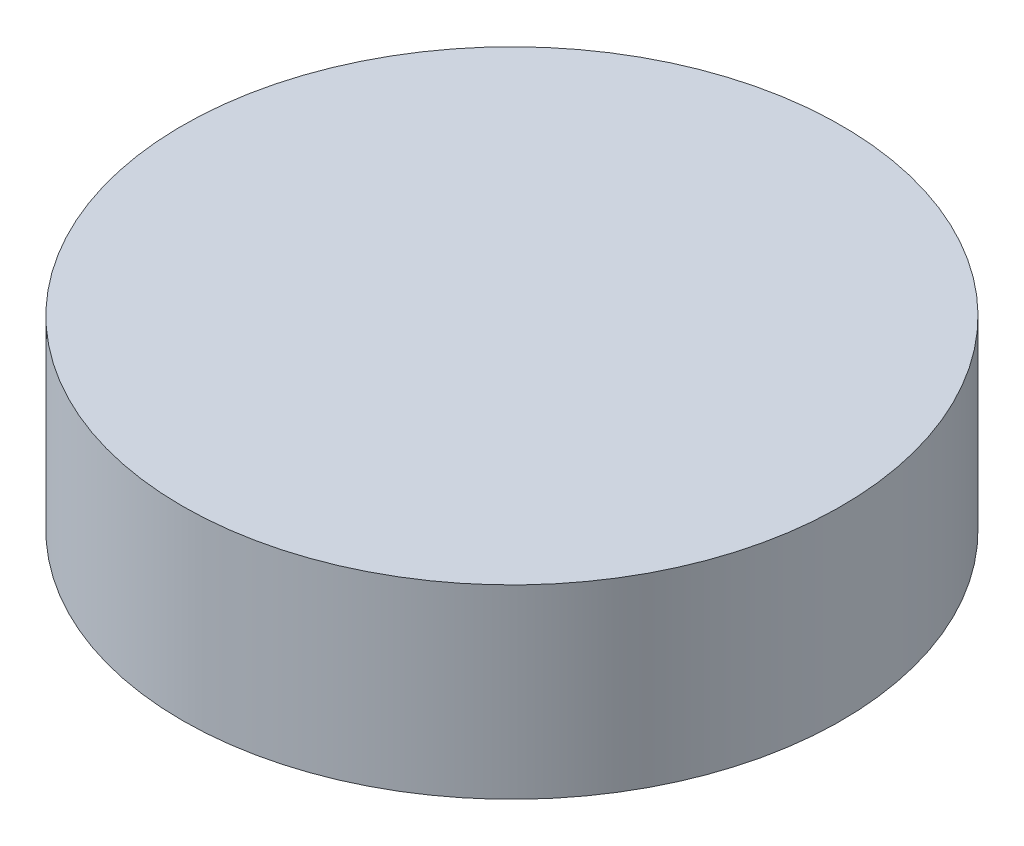
SolidWorks part; units mm, degrees
ref_plane "Ebene vorne" through (0, 0, 0) normal (0, 0, 1) x (1, 0, 0)
ref_plane "Ebene oben" through (0, 0, 0) normal (0, 1, 0) x (1, 0, 0)
ref_plane "Ebene rechts" through (0, 0, 0) normal (1, 0, 0) x (0, 0, -1)
sketch "Skizze1" plane through (0, 0, 0) normal (0, 1, 0) x (1, 0, 0)
  circle A0 centre (0, 0) radius 8.875
extrude "Aufsatz-Linear austragen1" add sketch "Skizze1" along normal blind 5
